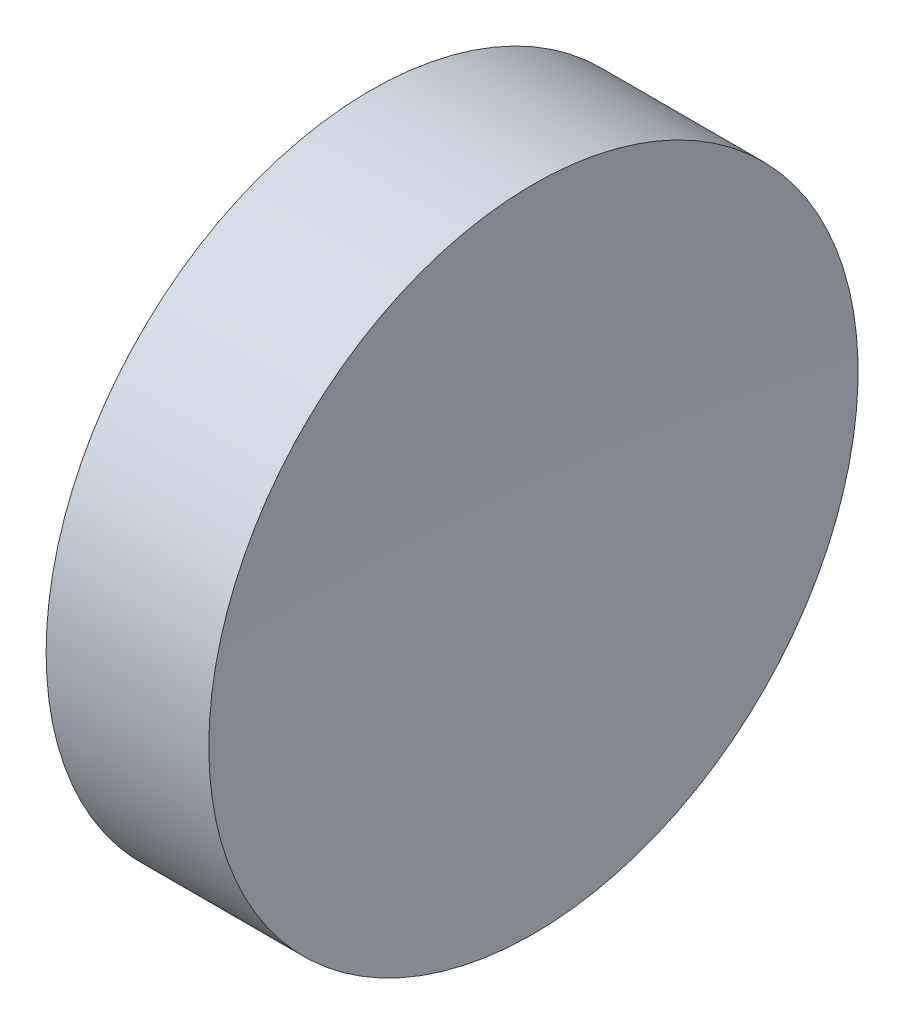
SolidWorks part; units mm, degrees
ref_plane "前视基准面" through (0, 0, 0) normal (0, 0, 1) x (1, 0, 0)
ref_plane "上视基准面" through (0, 0, 0) normal (0, 1, 0) x (1, 0, 0)
ref_plane "右视基准面" through (0, 0, 0) normal (1, 0, 0) x (0, 0, -1)
sketch "草图1" plane through (0, 0, 0) normal (0, 1, 0) x (1, 0, 0)
  line L0 (0, 0) -> (6.9328, 0) construction
  line L1 (0, 0) -> (2.98, 0)
  line L2 (0, 0) -> (0, 6.35)
  line L3 (0, 6.35) -> (3.1818, 6.35)
  arc A0 (3.1818, 6.35) -> (2.98, 0) centre (102.98, 0) ccw
  dimension "D3" = 100
  dimension "D1" = 2.98
  dimension "D2" = 6.35
revolve "旋转1" add sketch "草图1" angle 360 about L0
